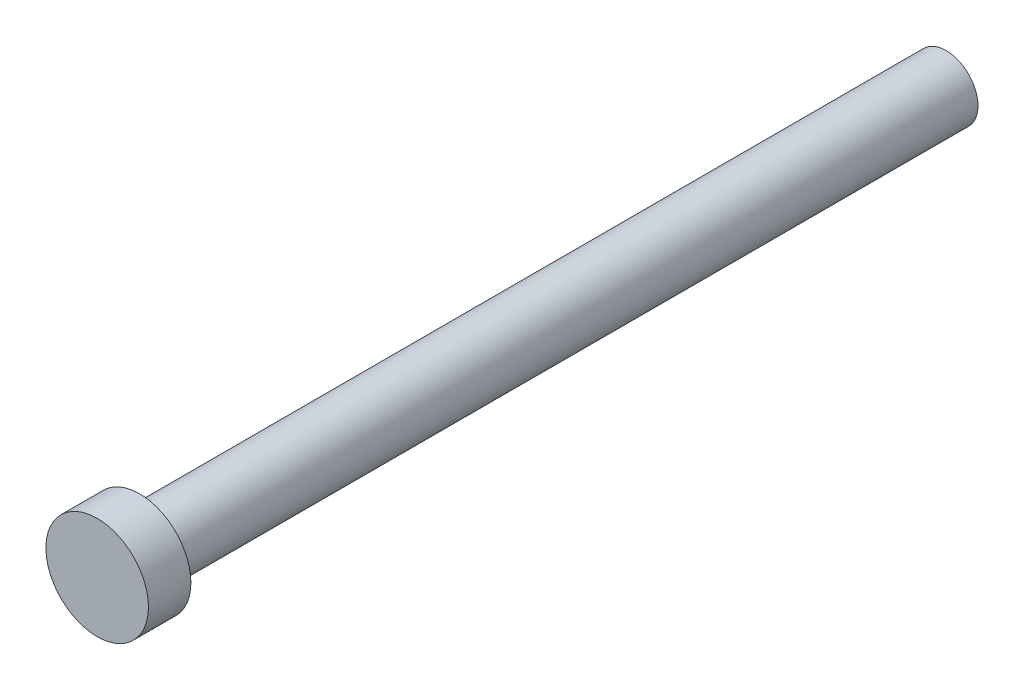
SolidWorks part; units mm, degrees
ref_plane "Front Plane" through (0, 0, 0) normal (0, 0, 1) x (1, 0, 0)
ref_plane "Top Plane" through (0, 0, 0) normal (0, 1, 0) x (1, 0, 0)
ref_plane "Right Plane" through (0, 0, 0) normal (1, 0, 0) x (0, 0, -1)
sketch "Sketch1" plane through (0, 0, 0) normal (0, 0, 1) x (1, 0, 0)
  circle A0 centre (0, 0) radius 1.5
  dimension "D1" = 3
extrude "Boss-Extrude1" add sketch "Sketch1" along normal blind 40
sketch "Sketch2" plane through (0, 0, 40) normal (0, 0, 1) x (1, 0, 0)
  circle A0 centre (0, 0) radius 2.4154
  circle A1 centre (0, 0) radius 1.5
extrude "Boss-Extrude2" add sketch "Sketch2" against normal blind 2
